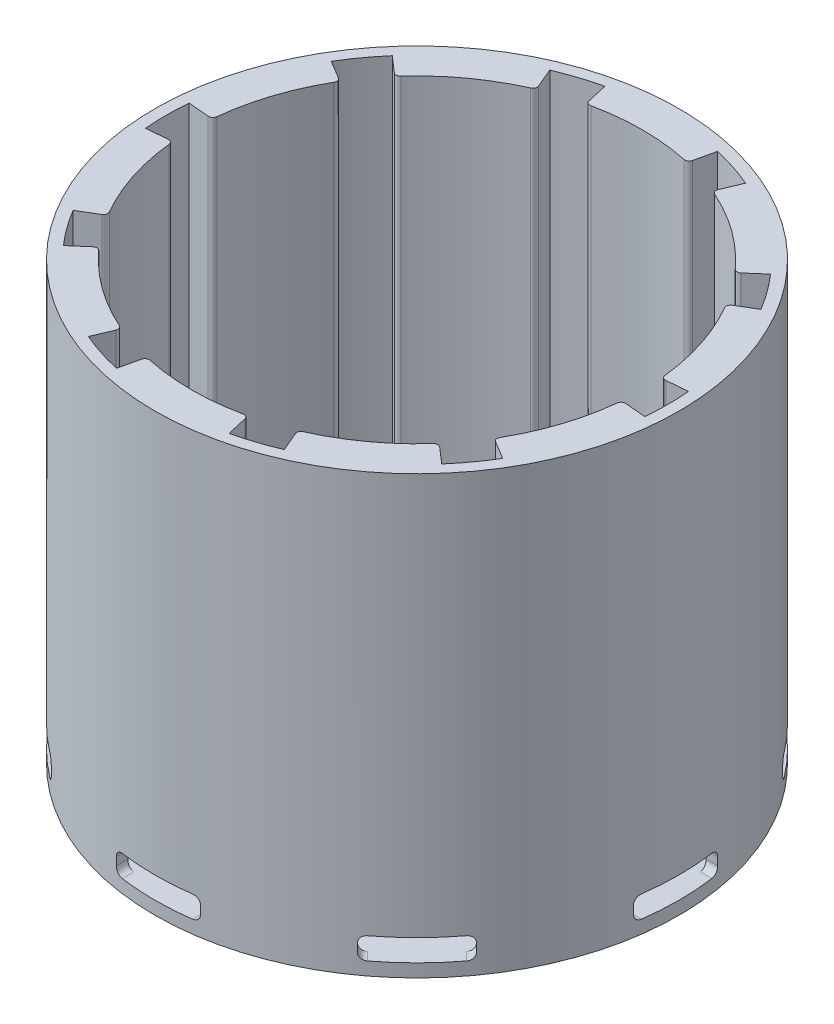
SolidWorks part; units mm, degrees
ref_plane "Front Plane" through (0, 0, 0) normal (0, 0, 1) x (1, 0, 0)
ref_plane "Top Plane" through (0, 0, 0) normal (0, 1, 0) x (1, 0, 0)
ref_plane "Right Plane" through (0, 0, 0) normal (1, 0, 0) x (0, 0, -1)
sketch "Sketch1" plane through (0, 0, 0) normal (0, 1, 0) x (1, 0, 0)
  line L1 (-30, 30) -> (30, 30)
  line L2 (-30, 30) -> (-30, -30)
  line L3 (-30, -30) -> (30, -30)
  line L4 (30, 30) -> (30, -30)
  line L5 (-30, 30) -> (30, -30) construction
  line L6 (-30, -30) -> (30, 30) construction
  circle A0 centre (0, 0) radius 30
  dimension "D1" = 60
  dimension "D2" = 60
extrude "Boss-Extrude2" add sketch "Sketch1" along normal blind 50 contours A0 L2 L3 | A0 | A0 L1 L2 | A0 L4 L1 | A0 L3 L4
sketch "Sketch2" plane through (0, 0, 30) normal (0, 0, 1) x (1, 0, 0)
  line L0 (0, 0) -> (0, 50) construction
  line L1 (-30, 50) -> (30, 50) construction
  line L2 (-4.025, 4) -> (4.025, 4)
  line L4 (4.825, 3.2) -> (4.825, 2.3)
  line L5 (-4.025, 1.5) -> (4.025, 1.5)
  line L6 (-4.825, 3.2) -> (-4.825, 2.3)
  arc A0 (-4.025, 1.5) -> (-4.825, 2.3) centre (-4.025, 2.3) cw
  arc A1 (4.825, 2.3) -> (4.025, 1.5) centre (4.025, 2.3) cw
  arc A2 (4.825, 3.2) -> (4.025, 4) centre (4.025, 3.2) ccw
  arc A3 (-4.025, 4) -> (-4.825, 3.2) centre (-4.025, 3.2) ccw
  dimension "D1" = 0.8
  dimension "D2" = 0.8
extrude "Cut-Extrude1" cut sketch "Sketch2" against normal blind 49.5
sketch "Sketch3" plane through (0, 50, 0) normal (0, 1, 0) x (1, 0, 0)
  circle A0 centre (0, 0) radius 30
  dimension "D1" = 60
extrude "Cut-Extrude2" cut sketch "Sketch3" against normal blind 50 flip side to cut
pattern_circular "CirPattern1" count 8 every 45 about axis through (0, 0, 0) along (0, 1, 0) of "Cut-Extrude1"
sketch "Sketch4" plane through (0, 50, 0) normal (0, 1, 0) x (1, 0, 0)
  circle A0 centre (0, 0) radius 25.8
extrude "Cut-Extrude3" cut sketch "Sketch4" against normal blind 48.5
sketch "Sketch5" plane through (0, 50, 0) normal (0, 1, 0) x (1, 0, 0)
  line L0 (0, 0) -> (0, 28.7) construction
  line L1 (0, 0) -> (28.7, 0) construction
  line L2 (0, 0) -> (6.4561, -27.9644) construction
  line L3 (0, -28.7) -> (0, 0) construction
  line L4 (0, 0) -> (-28.7, 0) construction
  line L5 (0, 0) -> (-6.4561, -27.9644) construction
  line L6 (-5.9151, -25.6213) -> (-6.4561, -27.9644)
  line L7 (5.9151, -25.6213) -> (6.4561, -27.9644)
  line L8 (19.8453, -17.2512) -> (21.6602, -18.8289)
  line L9 (10.2744, -24.2049) -> (11.214, -26.4185)
  line L10 (26.1952, -2.2918) -> (28.5908, -2.5014)
  line L11 (22.5394, -13.5431) -> (24.6007, -14.7816)
  line L12 (22.5394, 13.5431) -> (24.6007, 14.7816)
  line L13 (26.1952, 2.2918) -> (28.5908, 2.5014)
  line L14 (10.2744, 24.2049) -> (11.214, 26.4185)
  line L15 (19.8453, 17.2512) -> (21.6602, 18.8289)
  line L16 (-5.9151, 25.6213) -> (-6.4561, 27.9644)
  line L17 (5.9151, 25.6213) -> (6.4561, 27.9644)
  line L18 (-19.8453, 17.2512) -> (-21.6602, 18.8289)
  line L19 (-10.2744, 24.2049) -> (-11.214, 26.4185)
  line L20 (-26.1952, 2.2918) -> (-28.5908, 2.5014)
  line L21 (-22.5394, 13.5431) -> (-24.6007, 14.7816)
  line L22 (-22.5394, -13.5431) -> (-24.6007, -14.7816)
  line L23 (-26.1952, -2.2918) -> (-28.5908, -2.5014)
  line L24 (-10.2744, -24.2049) -> (-11.214, -26.4185)
  line L25 (-19.8453, -17.2512) -> (-21.6602, -18.8289)
  circle A0 centre (0, 0) radius 28.7
  circle A1 centre (0, 0) radius 25.8 construction
  arc A2 (-5.3248, -25.2445) -> (5.3248, -25.2445) centre (0, 0) ccw
  arc A3 (-6.4561, -27.9644) -> (6.4561, -27.9644) centre (0, 0) ccw
  arc A4 (-5.3248, -25.2445) -> (-5.9151, -25.6213) centre (-5.428, -25.7338) ccw
  arc A5 (5.9151, -25.6213) -> (5.3248, -25.2445) centre (5.428, -25.7338) ccw
  arc A6 (11.214, -26.4185) -> (21.6602, -18.8289) centre (0, 0) ccw
  arc A7 (19.8453, -17.2512) -> (19.1462, -17.2934) centre (19.5172, -17.6286) ccw
  arc A8 (10.5305, -23.5531) -> (19.1462, -17.2934) centre (0, 0) ccw
  arc A9 (10.5305, -23.5531) -> (10.2744, -24.2049) centre (10.7346, -24.0095) ccw
  arc A10 (24.6007, -14.7816) -> (28.5908, -2.5014) centre (0, 0) ccw
  arc A11 (26.1952, -2.2918) -> (25.6544, -2.7368) centre (26.1516, -2.7899) ccw
  arc A12 (22.3635, -12.8651) -> (25.6544, -2.7368) centre (0, 0) ccw
  arc A13 (22.3635, -12.8651) -> (22.5394, -13.5431) centre (22.7969, -13.1145) ccw
  arc A14 (28.5908, 2.5014) -> (24.6007, 14.7816) centre (0, 0) ccw
  arc A15 (22.5394, 13.5431) -> (22.3635, 12.8651) centre (22.7969, 13.1145) ccw
  arc A16 (25.6544, 2.7368) -> (22.3635, 12.8651) centre (0, 0) ccw
  arc A17 (25.6544, 2.7368) -> (26.1952, 2.2918) centre (26.1516, 2.7899) ccw
  arc A18 (21.6602, 18.8289) -> (11.214, 26.4185) centre (0, 0) ccw
  arc A19 (10.2744, 24.2049) -> (10.5305, 23.5531) centre (10.7346, 24.0095) ccw
  arc A20 (19.1462, 17.2934) -> (10.5305, 23.5531) centre (0, 0) ccw
  arc A21 (19.1462, 17.2934) -> (19.8453, 17.2512) centre (19.5172, 17.6286) ccw
  arc A22 (6.4561, 27.9644) -> (-6.4561, 27.9644) centre (0, 0) ccw
  arc A23 (-5.9151, 25.6213) -> (-5.3248, 25.2445) centre (-5.428, 25.7338) ccw
  arc A24 (5.3248, 25.2445) -> (-5.3248, 25.2445) centre (0, 0) ccw
  arc A25 (5.3248, 25.2445) -> (5.9151, 25.6213) centre (5.428, 25.7338) ccw
  arc A26 (-11.214, 26.4185) -> (-21.6602, 18.8289) centre (0, 0) ccw
  arc A27 (-19.8453, 17.2512) -> (-19.1462, 17.2934) centre (-19.5172, 17.6286) ccw
  arc A28 (-10.5305, 23.5531) -> (-19.1462, 17.2934) centre (0, 0) ccw
  arc A29 (-10.5305, 23.5531) -> (-10.2744, 24.2049) centre (-10.7346, 24.0095) ccw
  arc A30 (-24.6007, 14.7816) -> (-28.5908, 2.5014) centre (0, 0) ccw
  arc A31 (-26.1952, 2.2918) -> (-25.6544, 2.7368) centre (-26.1516, 2.7899) ccw
  arc A32 (-22.3635, 12.8651) -> (-25.6544, 2.7368) centre (0, 0) ccw
  arc A33 (-22.3635, 12.8651) -> (-22.5394, 13.5431) centre (-22.7969, 13.1145) ccw
  arc A34 (-28.5908, -2.5014) -> (-24.6007, -14.7816) centre (0, 0) ccw
  arc A35 (-22.5394, -13.5431) -> (-22.3635, -12.8651) centre (-22.7969, -13.1145) ccw
  arc A36 (-25.6544, -2.7368) -> (-22.3635, -12.8651) centre (0, 0) ccw
  arc A37 (-25.6544, -2.7368) -> (-26.1952, -2.2918) centre (-26.1516, -2.7899) ccw
  arc A38 (-21.6602, -18.8289) -> (-11.214, -26.4185) centre (0, 0) ccw
  arc A39 (-10.2744, -24.2049) -> (-10.5305, -23.5531) centre (-10.7346, -24.0095) ccw
  arc A40 (-19.1462, -17.2934) -> (-10.5305, -23.5531) centre (0, 0) ccw
  arc A41 (-19.1462, -17.2934) -> (-19.8453, -17.2512) centre (-19.5172, -17.6286) ccw
  point P9 (-5.8037, -25.1387)
  point P10 (5.8037, -25.1387)
  point P13 (0, -25.8)
  point P20 (-5.8037, -25.1387)
  point P23 (5.8037, -25.1387)
  point P98 (0, 0)
  circle M10 centre (0, 0) radius 25.8
  dimension "D1" = 13
  dimension "D2" = 0.5
  dimension "D4" = 57.4
  dimension "D3" = 10
extrude "Cut-Extrude5" cut sketch "Sketch5" against normal blind 48.5 contours A33 A27 L18 A0 L21 M10 | A29 A23 L16 A0 L19 M10 | A25 A19 L14 A0 L17 M10 | A21 A15 L12 A0 L15 M10 | A17 A11 L10 A0 L13 M10 | A13 A7 L8 A0 L11 M10 | A9 A5 L7 A0 L9 M10 | A39 L24 A0 L6 A4 M10 | A41 A35 L22 A0 L25 M10 | A37 A31 L20 A0 L23 M10
sketch "Sketch6" plane through (0, 1.5, 0) normal (0, 1, 0) x (1, 0, 0)
  circle A0 centre (0, 0) radius 28.7
  circle A1 centre (0, 0) radius 28.7 construction
extrude "Cut-Extrude6" cut sketch "Sketch6" along normal blind 4
sketch "Sketch12" plane through (0, 0, 0) normal (0, -1, 0) x (1, 0, 0)
  circle A0 centre (0, 0) radius 4
  dimension "D1" = 8
extrude "Cut-Extrude8" cut sketch "Sketch12" against normal blind 70
